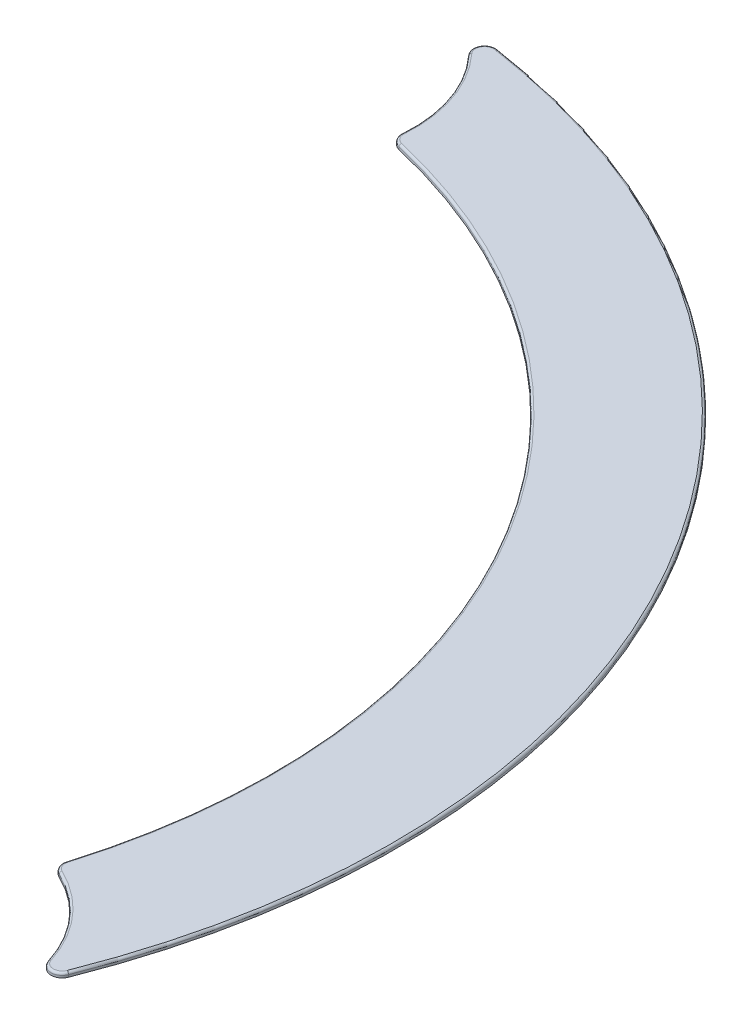
SolidWorks part; units mm, degrees
ref_plane "Front Plane" through (0, 0, 0) normal (0, 0, 1) x (1, 0, 0)
ref_plane "Top Plane" through (0, 0, 0) normal (0, 1, 0) x (1, 0, 0)
ref_plane "Right Plane" through (0, 0, 0) normal (1, 0, 0) x (0, 0, -1)
sketch "Sketch1" plane through (0, 0, 0) normal (0, 1, 0) x (1, 0, 0)
  line L0 (0, 0) -> (0, 28) construction
  line L1 (0, 0) -> (24.2487, -14) construction
  line L2 (18.3571, 19.7994) -> (18.867, 20.3494) construction
  line L3 (22.6065, 24.3826) -> (23.1164, 24.9326) construction
  circle A0 centre (0, 0) radius 27 construction
  circle A1 centre (0, 0) radius 34 construction
  arc A2 (5.9334, 27.1083) -> (3.1618, 33.0993) centre (0, 28) ccw
  arc A3 (30.2457, -13.8115) -> (26.4431, -8.4157) centre (24.2487, -14) ccw
  arc A4 (5.9334, 27.1083) -> (26.4431, -8.4157) centre (0, 0) cw
  arc A5 (30.2457, -13.8115) -> (3.1618, 33.0993) centre (0, 0) ccw
  dimension "D1" = 54
  dimension "D2" = 68
  dimension "D4" = 12
  dimension "D7" = 6
  dimension "D3" = 120
  dimension "D5" = 28
  dimension "D6" = 5.5
extrude "Boss-Extrude1" add sketch "Sketch1" along normal blind 0.2
fillet "Fillet1" radius 0.5 4 edges at (3.1618, 0.1, -33.0993) (5.9334, 0.1, -27.1083) (26.4431, 0.1, 8.4157) (30.2457, 0.1, 13.8115)
fillet "Fillet2" radius 0.1 8 edges at (4.3439, 0.2, -32.6325) (28.7953, 0.2, -16.625) (30.4325, 0.2, 12.5543) (28.7819, 0.2, 10.0693) (26.5957, 0.2, 8.3382) (24.0322, 0.2, -13.875) (6.0767, 0.2, -27.2017) (5.6707, 0.2, -29.9605)
